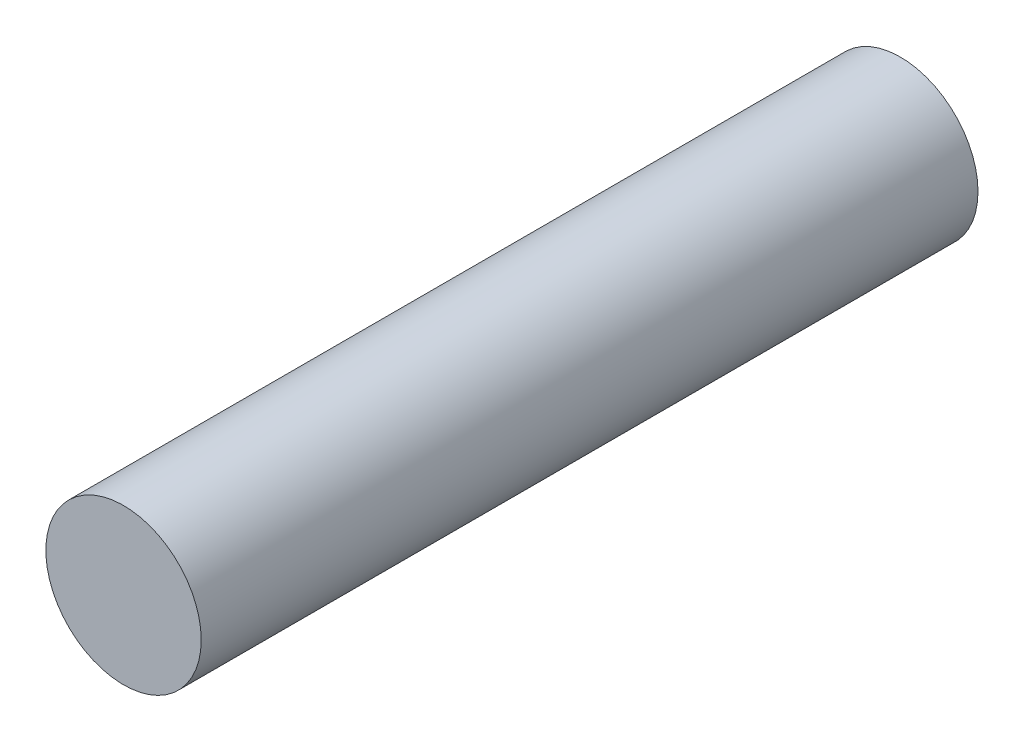
SolidWorks part; units mm, degrees
ref_plane "Front Plane" through (0, 0, 0) normal (0, 0, 1) x (1, 0, 0)
ref_plane "Top Plane" through (0, 0, 0) normal (0, 1, 0) x (1, 0, 0)
ref_plane "Right Plane" through (0, 0, 0) normal (1, 0, 0) x (0, 0, -1)
sketch "Sketch2" plane through (0, 0, 0) normal (0, 0, 1) x (1, 0, 0)
  circle A0 centre (0.0286, 0.0573) radius 2
  dimension "D1" = 4
extrude "Boss-Extrude1" add sketch "Sketch2" along normal blind 20
